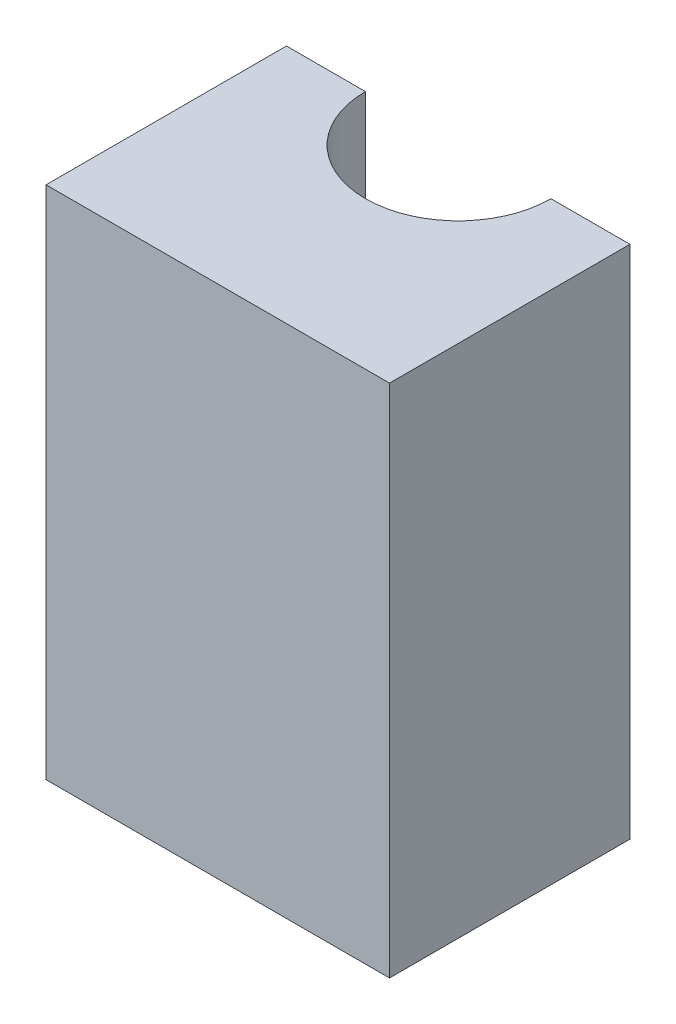
SolidWorks part; units mm, degrees
ref_plane "Front Plane" through (0, 0, 0) normal (0, 0, 1) x (1, 0, 0)
ref_plane "Top Plane" through (0, 0, 0) normal (0, 1, 0) x (1, 0, 0)
ref_plane "Right Plane" through (0, 0, 0) normal (1, 0, 0) x (0, 0, -1)
sketch "Sketch1" plane through (0, 0, 0) normal (0, 1, 0) x (1, 0, 0)
  line L0 (2.7, 3.5) -> (5, 3.5)
  line L1 (-5, -3.5) -> (5, -3.5)
  line L2 (-5, -3.5) -> (-5, 3.5)
  line L3 (-5, 3.5) -> (-2.7, 3.5)
  line L4 (5, -3.5) -> (5, 3.5)
  line L5 (-5, -3.5) -> (5, 3.5) construction
  line L6 (-5, 3.5) -> (5, -3.5) construction
  arc A0 (-2.7, 3.5) -> (2.7, 3.5) centre (0, 3.5) ccw
  point P0 (0, 0)
  dimension "D3" = 5.4
  dimension "D1" = 10
  dimension "D2" = 7
extrude "Boss-Extrude1" add sketch "Sketch1" along normal blind 15
